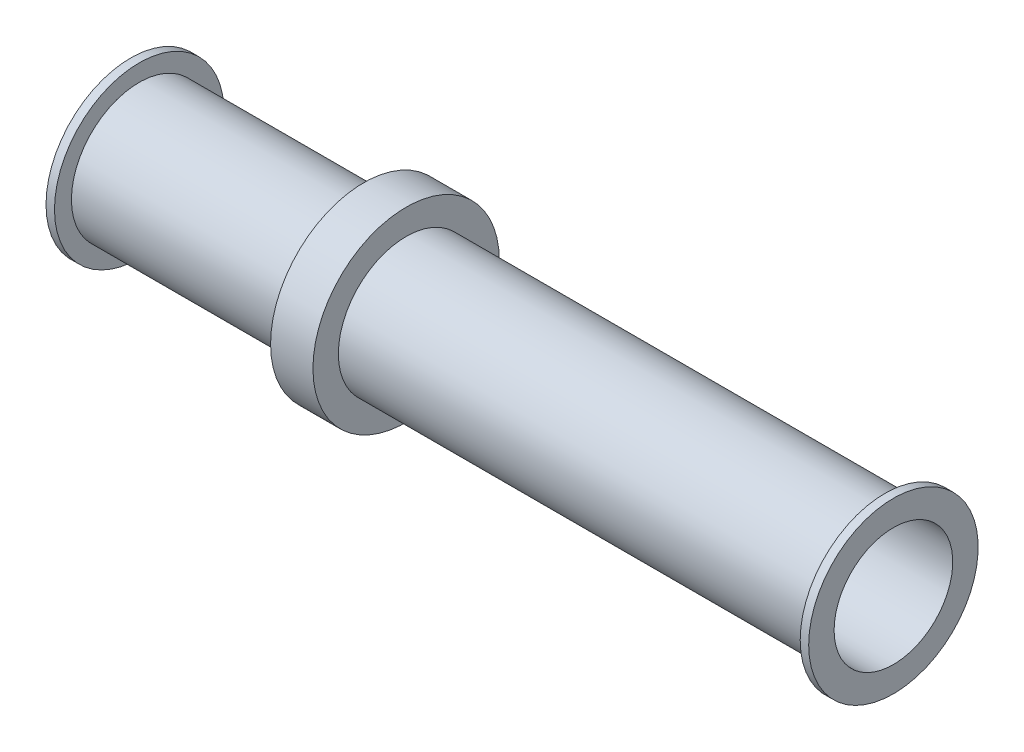
SolidWorks part; units mm, degrees
material "PVC Rigid"
ref_plane "Front Plane" through (0, 0, 0) normal (0, 0, 1) x (1, 0, 0)
ref_plane "Top Plane" through (0, 0, 0) normal (0, 1, 0) x (1, 0, 0)
ref_plane "Right Plane" through (0, 0, 0) normal (1, 0, 0) x (0, 0, -1)
sketch "Sketch1" plane through (0, 0, 0) normal (0, 0, 1) x (1, 0, 0)
  line L0 (0, 0) -> (87.134, 0) construction
  line L1 (0, 1.778) -> (0, 2.54)
  line L2 (0, 2.54) -> (0.254, 2.54)
  line L3 (0.254, 2.54) -> (0.254, 2.032)
  line L4 (0.254, 2.032) -> (6.985, 2.032)
  line L5 (8.255, 2.032) -> (8.255, 2.794)
  line L6 (8.255, 2.794) -> (6.985, 2.794)
  line L7 (6.985, 2.794) -> (6.985, 2.032)
  line L8 (8.255, 2.032) -> (22.606, 2.032)
  line L9 (22.606, 2.032) -> (22.606, 2.54)
  line L10 (22.606, 2.54) -> (22.86, 2.54)
  line L11 (22.86, 2.54) -> (22.86, 1.778)
  line L14 (0, 1.778) -> (22.86, 1.778)
  line L17 (7.62, 0) -> (7.62, 21.522) construction
  dimension "D1" = 7.62
  dimension "D2" = 0.254
  dimension "D3" = 1.27
  dimension "D4" = 22.86
  dimension "D5" = 0.254
  dimension "D6" = 2.794
  dimension "D7" = 1.778
  dimension "D8" = 2.54
  dimension "D9" = 0.254
revolve "Revolve1" add sketch "Sketch1" angle 360 about L0
